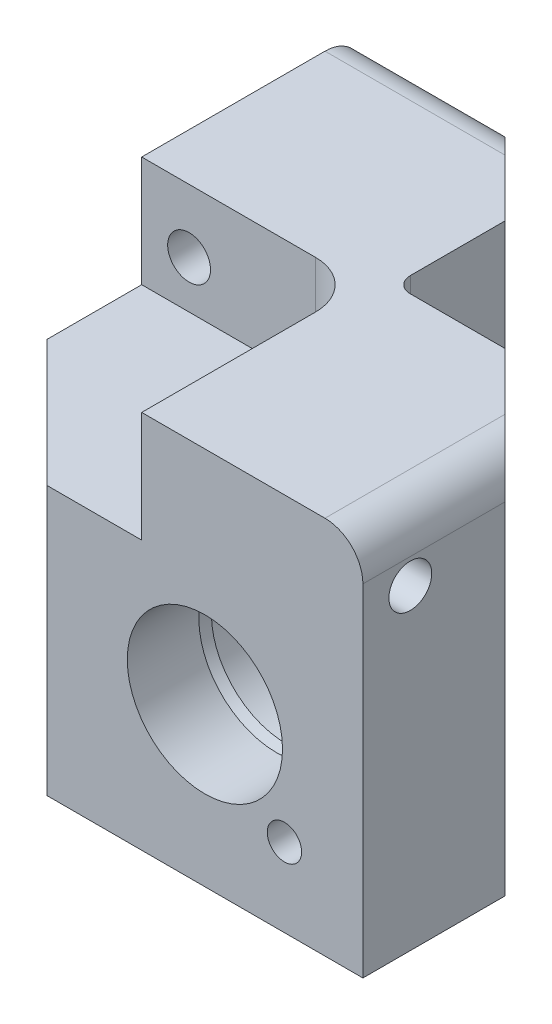
SolidWorks part; units mm, degrees
other "Markup1"
sketch "Sketch99" plane through (-25.4, 44.45, 25.4) normal (-0.9303, 0.3601, 0.0694) x (0.0764, 0.0053, 0.9971)
material "6061-T6 (SS)"
ref_plane "Front Plane" through (0, 0, 0) normal (0, 0, 1) x (1, 0, 0)
ref_plane "Top Plane" through (0, 0, 0) normal (0, 1, 0) x (1, 0, 0)
ref_plane "Right Plane" through (0, 0, 0) normal (1, 0, 0) x (0, 0, -1)
sketch "Sketch7" plane through (0, 0, 0) normal (0, 1, 0) x (1, 0, 0)
  line L0 (0, 0) -> (11.1125, 0)
  line L1 (20.6375, -9.525) -> (20.6375, -23.8125)
  line L2 (20.6375, -23.8125) -> (-23.8125, -23.8125)
  line L3 (-23.8125, -23.8125) -> (0, 0)
  line L4 (11.1125, 0) -> (20.6375, -9.525)
  dimension "D1" = 45
  dimension "D2" = 44.45
  dimension "D3" = 23.8125
  dimension "D4" = 14.2875
  dimension "D5" = 45
extrude "Boss-Extrude2" add sketch "Sketch7" along normal blind 38.1
sketch "Sketch22" plane through (0, 0, 23.8125) normal (0, 0, 1) x (1, 0, 0)
  line L1 (20.6375, 38.1) -> (20.6375, 0) construction
  line L2 (-23.8125, 0) -> (20.6375, 0) construction
  point P0 (4.7625, 15.875)
  dimension "D1" = 15.875
  dimension "D2" = 15.875
sketch "Sketch23" plane through (0, 0, 0) normal (0, 0, -1) x (-1, 0, 0)
  point P0 (-4.7625, 15.875)
curve "Curve3"
sketch3d "3DSketch6"
  line L0 (4.7625, 15.875, 23.8125) -> (4.7625, 15.875, 0) construction
sketch "Sketch24" plane through (4.7625, 0, 0) normal (-1, 0, 0) x (0, 0, 1)
  line L0 (23.8125, 15.875) -> (23.8125, 23.6728)
  line L1 (23.8125, 23.6728) -> (16.6243, 23.6728)
  line L2 (16.6243, 23.6728) -> (15.629, 23.4061)
  line L3 (15.629, 23.4061) -> (9.8679, 23.4061)
  line L4 (9.6647, 23.2029) -> (9.6647, 19.7485)
  line L5 (9.2248, 19.4945) -> (6.3627, 19.4945)
  line L6 (6.1595, 19.2913) -> (6.1595, 16.375)
  line L7 (6.1595, 16.375) -> (4.703, 16.524)
  line L8 (4.703, 16.524) -> (1.4605, 17.3928)
  line L9 (1.4605, 17.3928) -> (1.4605, 15.875)
  line L10 (1.4605, 15.875) -> (23.8125, 15.875)
  line L11 (9.6647, 19.7485) -> (9.2248, 19.4945)
  arc A0 (9.8679, 23.4061) -> (9.6647, 23.2029) centre (9.8679, 23.2029) ccw
  arc A1 (6.3627, 19.4945) -> (6.1595, 19.2913) centre (6.3627, 19.2913) ccw
  dimension "D3" = 0.2032
  dimension "D9" = 0.2032
  dimension "D1" = 7.7978
  dimension "D2" = 7.5311
  dimension "D4" = 7.1882
  dimension "D5" = 15
  dimension "D6" = 14.1478
  dimension "D7" = 30
  dimension "D8" = 3.6195
  dimension "D10" = 17.653
  dimension "D11" = 0.5
  dimension "D12" = 5.84
  dimension "D13" = 15
  dimension "D14" = 0.649
  dimension "D15" = 22.352
  dimension "D16" = 0.254
revolve "Port Manifold" cut sketch "Sketch24" angle 360 about L10
fillet "Fillet3" radius 0.127 1 edges at (4.2625, 15.875, 6.1595)
hole_wizard "#8-32 Tapped Hole1" positions "Sketch26" profile "Sketch27" tap size "#8-32" standard "ANSI Inch"
sketch "Sketch26" plane through (0, 0, 23.8125) normal (0, 0, 1) x (1, 0, 0)
  line L0 (4.7625, 15.875) -> (12.7549, 7.8826) construction
  line L2 (4.7625, 15.875) -> (4.7625, 4.572) construction
  circle A0 centre (4.7625, 15.875) radius 11.303
  point P0 (12.7549, 7.8826)
  dimension "D1" = 22.606
  dimension "D2" = 45
sketch "Sketch27" plane through (12.7549, 7.8826, 23.8125) normal (1, 0, 0) x (0, -1, 0)
  line L0 (0, 0) -> (0, 11.1978)
  line L1 (0, 11.1978) -> (1.7272, 10.16)
  line L2 (1.7272, 10.16) -> (1.7272, 0)
  line L5 (1.7272, 0) -> (0, 0)
  line L10 (0, 11.1978) -> (-1.7272, 10.16) construction
  line L11 (0, -6.35) -> (0, 107.95) construction
  dimension "Tap Drill Dia." = 3.4544
  dimension "Tap Drill Depth" = 10.16
  dimension "Drill Angle" = 118
cosmetic thread "Hole Thread1" parameters "D1"=8.382, "D2"=4.1656
hole_wizard "9/64 (0.14063) Diameter Hole1" positions "Sketch88" profile "Sketch90" hole size "9/64" standard "ANSI Inch"
sketch "Sketch88" plane through (0, 0, 0) normal (0, 0, -1) x (-1, 0, 0)
  point P0 (-4.7625, 15.875)
sketch "Sketch90" plane through (4.7625, 15.875, 0) normal (1, 0, 0) x (0, 1, 0)
  line L0 (0, 0) -> (0, 3.81)
  line L1 (0, 3.81) -> (1.786, 2.7369)
  line L2 (1.786, 2.7369) -> (1.786, 0)
  line L5 (1.786, 0) -> (0, 0)
  line L10 (0, 3.81) -> (-1.786, 2.7369) construction
  line L11 (0, -6.35) -> (0, 107.95) construction
  dimension "Hole Dia." = 3.572
  dimension "Hole Depth" = 3.81
  dimension "Drill Angle" = 118
mirror "Mirror6" of "9/64 (0.14063) Diameter Hole1", "Port Manifold", "#8-32 Tapped Hole1", "Boss-Extrude2"
cosmetic thread "Hole Thread2" parameters "D1"=8.382, "D2"=4.1656
fillet "Fillet16" radius 3.81 2 edges at (-16.6687, 38.1, -20.6375) (20.6375, 38.1, 16.6687)
sketch "Sketch93" plane through (0, 38.1, 0) normal (0, 1, 0) x (1, 0, 0)
  line L1 (-23.8125, -23.8125) -> (-1.5875, -23.8125)
  line L2 (-23.8125, -23.8125) -> (-23.8125, -1.5875)
  line L3 (-23.8125, -1.5875) -> (-6.35, -1.5875)
  line L4 (-1.5875, -23.8125) -> (-1.5875, -6.35)
  line L5 (-23.8125, -23.8125) -> (-23.8125, 16.8275) construction
  line L7 (-23.8125, -23.8125) -> (16.8275, -23.8125) construction
  arc A0 (-6.35, -1.5875) -> (-1.5875, -6.35) centre (-6.35, -6.35) cw
  dimension "D2" = 4.7625
  dimension "D3" = 22.225
extrude "Cut-Extrude3" cut sketch "Sketch93" against normal blind 11.1125
hole_wizard "#18 (0.1695) Diameter Hole1" positions "Sketch97" profile "Sketch98" hole size "#18" standard "ANSI Inch" end condition through all
sketch "Sketch97" plane through (-1.5875, 0, 0) normal (-1, 0, 0) x (0, 0, 1)
  line L0 (23.8125, 31.75) -> (19.05, 31.75) construction
  line L2 (23.8125, 26.9875) -> (6.35, 26.9875) construction
  point P2 (19.05, 31.75)
  dimension "D1" = 4.7625
  dimension "D2" = 4.7625
sketch "Sketch98" plane through (-1.5875, 31.75, 19.05) normal (0, 1, 0) x (0, 0, 1)
  line L0 (0, 0) -> (0, 22.225)
  line L1 (0, 22.225) -> (2.1526, 22.225)
  line L2 (2.1526, 22.225) -> (2.1526, 0)
  line L5 (2.1526, 0) -> (0, 0)
  line L11 (0, -6.35) -> (0, 107.95) construction
  dimension "Thru Hole Dia." = 4.3053
  dimension "Thru Hole Depth" = 22.225
ref_plane "Plane1" through (0, 0, 0) normal (0.7071, 0, 0.7071) x (0.7071, 0, -0.7071)
ref_plane "Plane2" through (0, 15.875, 0) normal (0, 1, 0) x (1, 0, 0)
mirror "Mirror9" about plane through (0, 0, 0) normal (0.7071, 0, 0.7071) of "#18 (0.1695) Diameter Hole1"
sketch "Sketch101" plane through (0, 0, 0) normal (0, -1, 0) x (1, 0, 0)
  line L0 (0, 0) -> (-23.8125, 23.8125) construction
  line L1 (-23.8125, 23.8125) -> (20.6375, 23.8125) construction
  circle A0 centre (-9.8425, 9.8425) radius 2.54
  dimension "D1" = 5.08
  dimension "D2" = 13.97
extrude "Cut-Extrude4" cut sketch "Sketch101" against normal blind 17.78
sketch "Sketch102" plane through (0, 15.875, 0) normal (0, 1, 0) x (1, 0, 0)
  line L0 (-0.4445, -9.3345) -> (-9.176, -9.3345) construction
  line L5 (-0.4445, -9.3345) -> (-10.6045, -9.3345)
  line L6 (-0.4445, -9.3345) -> (-0.4445, -10.6045)
  line L7 (-0.4445, -10.6045) -> (-10.6045, -10.6045)
  line L8 (-10.6045, -9.3345) -> (-10.6045, -10.6045)
  dimension "D1" = 5.207
  dimension "D2" = 14.478
  dimension "D3" = 13.208
  dimension "D4" = 10.16
revolve "Cut-Revolve1" cut sketch "Sketch102" angle 360 about L0
mirror "Mirror10" about plane through (0, 0, 0) normal (0.7071, 0, 0.7071) of "Cut-Revolve1"
chamfer "Chamfer1" distance 12.7 1 edges at (-23.8125, 13.4938, 23.8125)
fillet "Fillet17" radius 1.5875 1 edges at (0, 19.05, 0)
hole_wizard "1/8 NPT Tapped Hole1" positions "Sketch103" profile "Sketch104" size "1/8" standard "ANSI Inch"
sketch "Sketch103" plane through (0, 0, 0) normal (0, -1, 0) x (-1, 0, 0)
  point P0 (9.8425, -9.8425)
sketch "Sketch104" plane through (-9.8425, 0, 9.8425) normal (1, 0, 0) x (0, 0, -1)
  line L0 (0, 0) -> (0, 11.684)
  line L1 (4.2164, 9.1505) -> (0, 11.684)
  line L2 (-4.2164, 9.1505) -> (0, 11.684) construction
  line L3 (4.2164, 9.1505) -> (4.2164, 6.858)
  line L4 (4.2164, 6.858) -> (4.5374, 6.858)
  line L5 (4.5374, 6.858) -> (4.7427, 0)
  line L6 (-4.5374, 6.858) -> (-4.7427, 0) construction
  line L7 (4.7427, 0) -> (0, 0)
  line L8 (0, -6.35) -> (0, 107.95) construction
  line L11 (-4.2164, 6.858) -> (-4.5374, 6.858) construction
  dimension "Tap Drill Dia." = 8.4328
  dimension "Tap Drill Depth" = 11.684
  dimension "Thread Dia." = 9.4855
  dimension "Thread Angle" = 3.43
  dimension "Thread Depth" = 6.858
  dimension "Drill Angle" = 118
cosmetic thread "Hole Thread3" parameters "D1"=6.858, "D2"=10.2827
